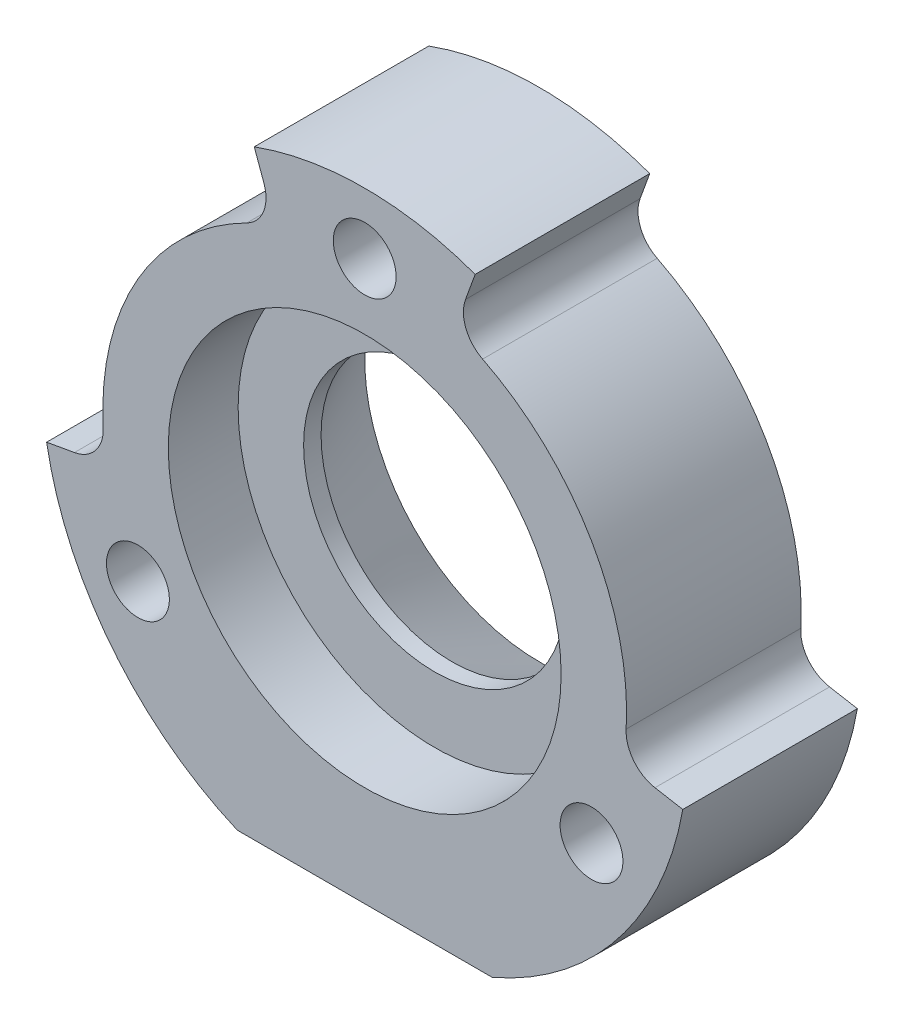
SolidWorks part; units mm, degrees
ref_plane "前视基准面" through (0, 0, 0) normal (0, 0, 1) x (1, 0, 0)
ref_plane "上视基准面" through (0, 0, 0) normal (0, 1, 0) x (1, 0, 0)
ref_plane "右视基准面" through (0, 0, 0) normal (1, 0, 0) x (0, 0, -1)
ref_plane "基准面4" through (0, 0, 10) normal (0, 0, 1) x (1, 0, 0)
sketch "草图1" plane through (0, 0, 10) normal (0, 0, 1) x (1, 0, 0)
  line L0 (-457.2973, 133) -> (-442.7027, 133)
  arc A0 (-442.7027, 133) -> (-457.2973, 133) centre (-450, 150) ccw
extrude "凸台-拉伸1" add sketch "草图1" against normal blind 10
sketch "草图2" plane through (0, 0, 0) normal (0, 0, -1) x (-1, 0, 0)
  line L0 (431.7811, 146.7875) -> (435.2279, 147.3953)
  line L1 (444.8697, 164.0954) -> (443.6726, 167.3843)
  arc A0 (435.2279, 147.3953) -> (444.8697, 164.0954) centre (450, 150) cw
  arc A1 (443.6726, 167.3843) -> (431.7811, 146.7875) centre (450, 150) ccw
extrude "切除-拉伸1" cut sketch "草图2" against normal through all
sketch "草图3" plane through (0, 0, 0) normal (0, 0, -1) x (-1, 0, 0)
  line L0 (456.3274, 167.3843) -> (455.1303, 164.0954)
  line L1 (464.7721, 147.3953) -> (468.2189, 146.7875)
  arc A0 (455.1303, 164.0954) -> (464.7721, 147.3953) centre (450, 150) cw
  arc A1 (468.2189, 146.7875) -> (456.3274, 167.3843) centre (450, 150) ccw
extrude "切除-拉伸2" cut sketch "草图3" against normal through all
hole_wizard "Ø3.6 (3.6) 直径孔1" positions "草图5" profile "草图4" hole size "Ø3.6" standard "ANSI Metric"
sketch "草图5" plane through (0, 0, 0) normal (0, 0, -1) x (-1, 0, 0)
  point P0 (437.0096, 142.5)
  point P1 (450, 165)
  point P2 (462.9904, 142.5)
sketch "草图4" plane through (-437.0096, 142.5, 0) normal (1, 0, 0) x (0, 1, 0)
  line L0 (0, 0) -> (0, 10)
  line L1 (0, 10) -> (1.8, 10)
  line L2 (1.8, 10) -> (1.8, 0)
  line L5 (1.8, 0) -> (0, 0)
  line L11 (0, -6.35) -> (0, 107.95) construction
  dimension "通孔孔直径" = 3.6
  dimension "通孔孔深度" = 10
hole_wizard "M12 六角头螺栓的柱形沉头孔1" positions "草图7" profile "草图6" counterbore size "M12" standard "ANSI Metric"
sketch "草图7" plane through (0, 0, 10) normal (0, 0, 1) x (1, 0, 0)
  point P0 (-450, 150)
sketch "草图6" plane through (-450, 150, 10) normal (1, 0, 0) x (0, -1, 0)
  line L0 (0, 0) -> (0, 10)
  line L1 (7.5, 5) -> (10, 10)
  line L2 (7.5, 5) -> (7.5, 4)
  line L3 (7.5, 4) -> (11.25, 4)
  line L4 (11.25, 4) -> (11.25, 0)
  line L5 (11.25, 0) -> (0, 0)
  line L11 (0, -6.35) -> (0, 107.95) construction
  line L12 (10, 10) -> (0, 10)
  line L13 (-7.5, 5) -> (-10, 10) construction
  dimension "通孔孔直径" = 15
  dimension "通孔孔深度" = 10
  dimension "柱形沉头孔直径" = 22.5
  dimension "柱形沉头孔深度" = 4
  dimension "远端锥形沉头孔直径" = 20
  dimension "远端锥形沉头孔角度" = 53.13
fillet "圆角1" radius 2 4 edges at (-435.2279, 147.3953, 5) (-444.8697, 164.0954, 5) (-464.7721, 147.3953, 5) (-455.1303, 164.0954, 5)
